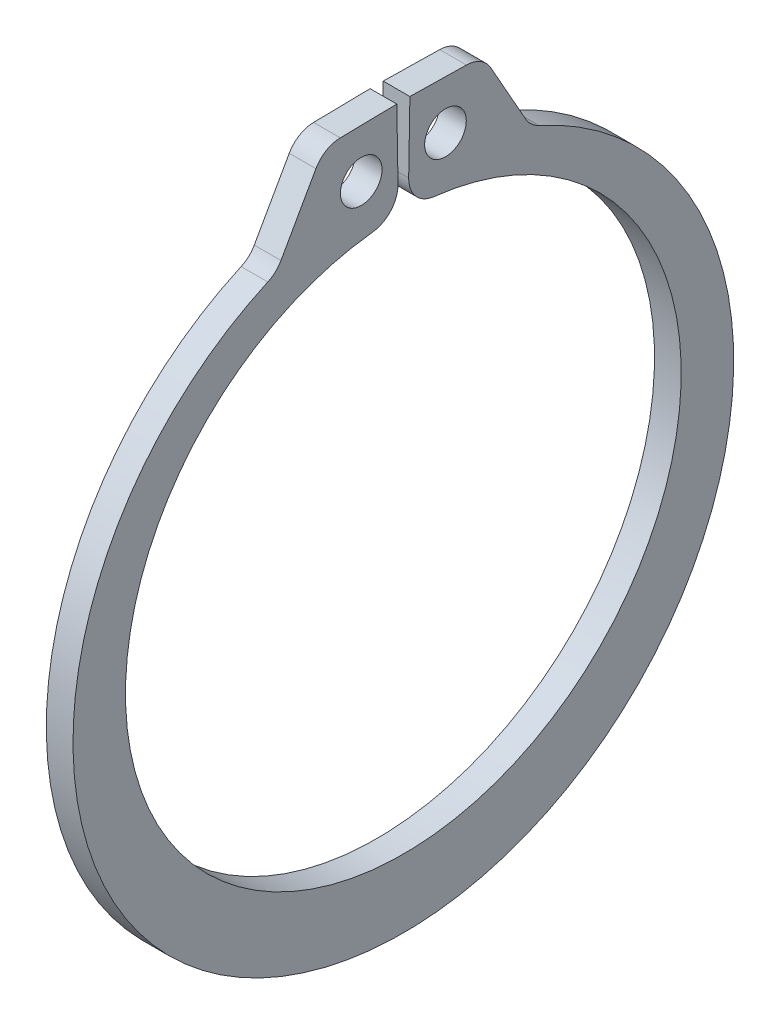
SolidWorks part; units mm, degrees
material "AISI 1085 Steel (Piano Wire)"
ref_plane "Front" through (0, 0, 0) normal (0, 0, 1) x (1, 0, 0)
ref_plane "Top" through (0, 0, 0) normal (0, 1, 0) x (1, 0, 0)
ref_plane "Right" through (0, 0, 0) normal (1, 0, 0) x (0, 0, -1)
sketch "Sketch1" plane through (0, 0, 0) normal (1, 0, 0) x (0, 0, -1)
  line L0 (0, 0) -> (0, 13.2207) construction
  line L1 (-0.2307, 13.2187) -> (-0.3114, 17.8408)
  line L2 (0.3114, 17.8408) -> (3.778, 17.7803)
  line L3 (3.778, 17.7803) -> (6.0478, 13.7531)
  line L4 (0.2307, 13.2187) -> (0.3114, 17.8408)
  line L5 (-0.3114, 17.8408) -> (-3.778, 17.7803)
  line L6 (-3.778, 17.7803) -> (-6.0478, 13.7531)
  line L7 (-6.0478, 13.7531) -> (-5.3219, 12.1023) construction
  line L8 (6.0478, 13.7531) -> (5.3219, 12.1023) construction
  line L9 (0, -13.2207) -> (0, -16.4719) construction
  line L10 (-3.778, 17.7803) -> (-0.2307, 13.2187) construction
  line L11 (0, 13.2207) -> (0, 17.8435) construction
  line L12 (-13.2207, 0) -> (13.2207, 0) construction
  circle A0 centre (0, 0) radius 13.2207 construction
  arc A1 (-0.2307, 13.2187) -> (0.2307, 13.2187) centre (0, 0) ccw
  circle A4 centre (-2.0044, 15.4995) radius 0.9906
  circle A5 centre (2.0044, 15.4995) radius 0.9906
  arc A6 (-6.0478, 13.7531) -> (6.0478, 13.7531) centre (0, -0.7543) ccw construction
  point P0 (0, -16.4719)
  dimension "Ring ID" = 26.4414
  dimension "Hole Diameter" = 1.9812
  dimension "Min. Sec." = 1.8034
  dimension "Max. Sec." = 3.2512
  dimension "Lug Height" = 4.6228
  dimension "D2" = 3.4671
  dimension "Angle" = 1
sketch "Sketch2" plane through (0, 0, 0) normal (0, 1, 0) x (1, 0, 0)
  line L0 (-0.635, -15.6994) -> (0.635, -15.6994) construction
  line L1 (0, -15.7176) -> (0, 15.7176) construction
  point P8 (0, -15.6994)
  dimension "Ring Thickness" = 1.27
sketch "Sketch3" plane through (0, 0, 0) normal (1, 0, 0) x (0, 0, -1)
  line L0 (-3.778, 17.7803) -> (-6.0478, 13.7531) construction
  line L1 (-3.778, 17.7803) -> (-6.0478, 13.7531)
  line L2 (-0.3114, 17.8408) -> (-3.778, 17.7803) construction
  line L3 (-0.3114, 17.8408) -> (-3.778, 17.7803)
  line L4 (-0.2307, 13.2187) -> (-0.3114, 17.8408) construction
  line L5 (-0.2307, 13.2187) -> (-0.3114, 17.8408)
  line L6 (0.2307, 13.2187) -> (0.3114, 17.8408) construction
  line L7 (0.2307, 13.2187) -> (0.3114, 17.8408)
  line L8 (0.3114, 17.8408) -> (3.778, 17.7803) construction
  line L9 (0.3114, 17.8408) -> (3.778, 17.7803)
  line L10 (3.778, 17.7803) -> (6.0478, 13.7531) construction
  line L11 (3.778, 17.7803) -> (6.0478, 13.7531)
  arc A0 (-6.0478, 13.7531) -> (6.0478, 13.7531) centre (0, -0.7543) ccw construction
  arc A1 (-6.0478, 13.7531) -> (6.0478, 13.7531) centre (0, -0.7543) ccw
  arc A2 (-0.2307, 13.2187) -> (0.2307, 13.2187) centre (0, 0) ccw construction
  arc A3 (-0.2307, 13.2187) -> (0.2307, 13.2187) centre (0, 0) ccw
  circle A4 centre (-2.0044, 15.4995) radius 0.9906 construction
  circle A5 centre (-2.0044, 15.4995) radius 0.9906
  circle A6 centre (2.0044, 15.4995) radius 0.9906 construction
  circle A7 centre (2.0044, 15.4995) radius 0.9906
extrude "Boss-Extrude1" add sketch "Sketch3" along normal up to vertex (0.635 mm away) and the other way up to vertex (0.635 mm away) up to point (0.635, 0, 15.6994) other way up to point (-0.635, 0, 15.6994)
fillet "Fillet1" radius 1.3589 6 edges at (0, 13.7531, -6.0478) (0, 17.7803, -3.778) (0, 13.2187, -0.2307) (0, 13.2187, 0.2307) (0, 17.7803, 3.778) (0, 13.7531, 6.0478)
sketch "Sketch4" plane through (0, 0, 0) normal (1, 0, 0) x (0, 0, -1)
  line L0 (-11.4495, 6.6104) -> (0, 0) construction
  line L1 (0, 0) -> (0, 13.2207) construction
  line L2 (0, 17.8435) -> (0, 13.2207) construction
  arc A0 (-0.2307, 13.2187) -> (0.2307, 13.2187) centre (0, 0) ccw construction
  point P0 (0, 0)
  point P1 (-11.4495, 6.6104)
  dimension "D1" = 60
equation "\"D2@Sketch1\" = \"Lug Height@Sketch1\" * .75"
